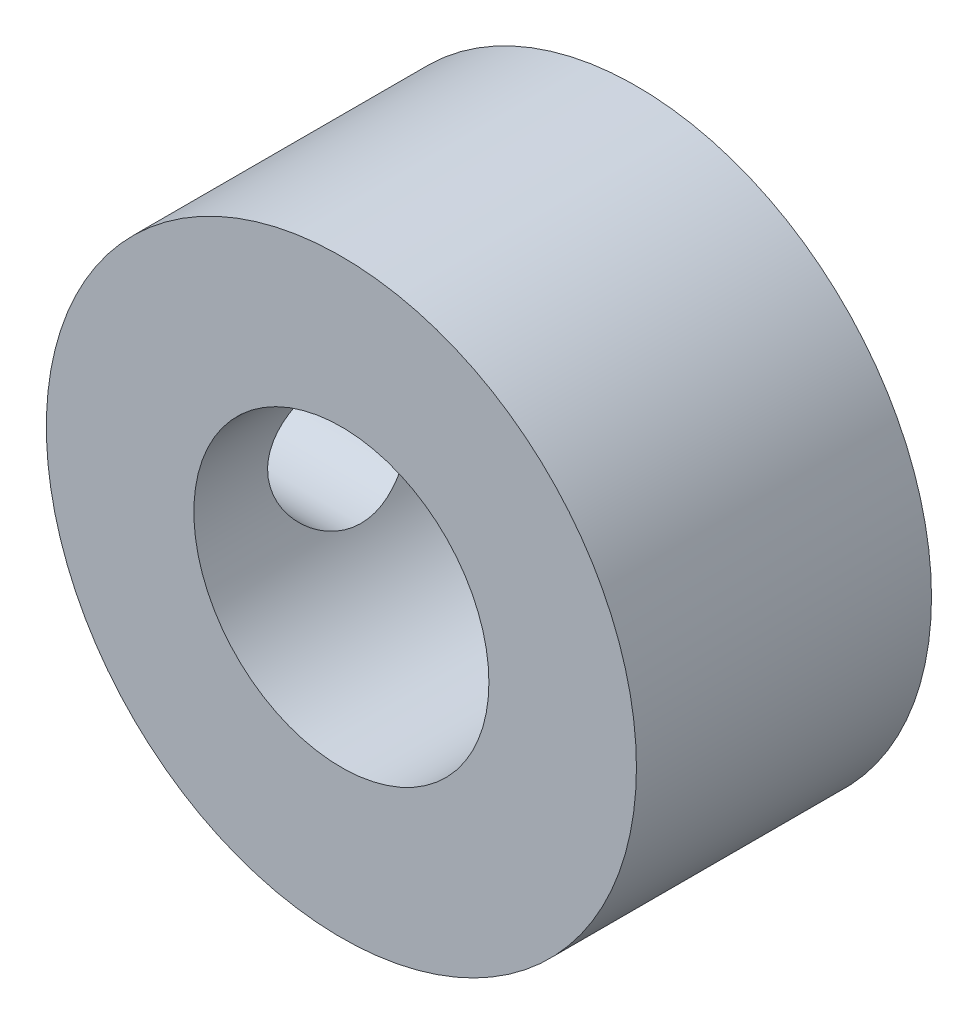
SolidWorks part; units mm, degrees
ref_plane "Front Plane" through (0, 0, 0) normal (0, 0, 1) x (1, 0, 0)
ref_plane "Top Plane" through (0, 0, 0) normal (0, 1, 0) x (1, 0, 0)
ref_plane "Right Plane" through (0, 0, 0) normal (1, 0, 0) x (0, 0, -1)
sketch "Sketch1" plane through (0, 0, 0) normal (0, 0, 1) x (1, 0, 0)
  circle A0 centre (0, 0) radius 2.5
  circle A1 centre (0, 0) radius 5
  dimension "D1" = 5
  dimension "D2" = 10
extrude "Boss-Extrude1" add sketch "Sketch1" along normal blind 5
sketch "Sketch2" plane through (0, 0, 0) normal (1, 0, 0) x (0, 0, -1)
  line L0 (-2.5, -5) -> (-2.5, 0) construction
  line L1 (-5, -5) -> (0, -5) construction
  circle A0 centre (-2.5, 0) radius 1.25
  dimension "D1" = 2.5
extrude "Cut-Extrude1" cut sketch "Sketch2" against normal through all
